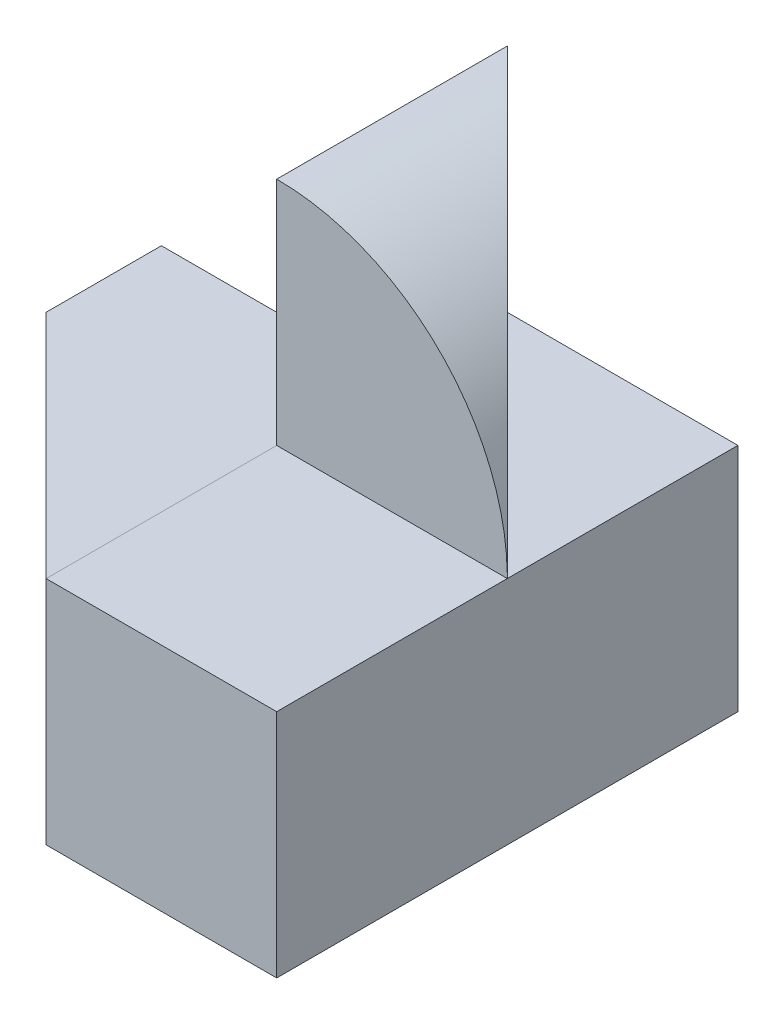
SolidWorks part; units mm, degrees
ref_plane "Front" through (0, 0, 0) normal (0, 0, 1) x (1, 0, 0)
ref_plane "Top" through (0, 0, 0) normal (0, 1, 0) x (1, 0, 0)
ref_plane "Right" through (0, 0, 0) normal (1, 0, 0) x (0, 0, -1)
sketch "Sketch1" plane through (0, 0, 0) normal (0, 1, 0) x (1, 0, 0)
  line L1 (-2, -2) -> (2, -2)
  line L2 (-2, -2) -> (-2, 2)
  line L3 (-2, 2) -> (2, 2)
  line L4 (2, -2) -> (2, 2)
  line L5 (-2, -2) -> (2, 2) construction
  line L6 (-2, 2) -> (2, -2) construction
  point P0 (0, 0)
  dimension "D1" = 4
  dimension "D2" = 4
extrude "Boss-Extrude1" add sketch "Sketch1" along normal blind 4
sketch "Sketch2" plane through (0, 0, 2) normal (0, 0, 1) x (1, 0, 0)
  line L0 (2, 4) -> (2, 0) construction
  line L1 (-2, 4) -> (2, 4) construction
  line L2 (0, 4) -> (0.0003, 2)
  line L3 (0.0003, 2) -> (-2, 2)
  line L4 (-2, 4) -> (-2, 0) construction
  line L5 (-2, 2) -> (-2, 4)
  line L6 (-2, 4) -> (2, 4)
  line L7 (2, 4) -> (2, 2.0349)
  arc A0 (2, 2.0349) -> (0, 4) centre (0.0003, 2) ccw
  line M2 (2, 0) -> (2, 4)
  line M3 (2, 4) -> (-2, 4)
  line M4 (-2, 4) -> (-2, 0)
  dimension "D1" = 2
extrude "Cut-Extrude1" cut sketch "Sketch2" against normal blind 4 contours L3 L2 M3 M4 | A0 M2 M3
sketch "Sketch3" plane through (0, 2, 0) normal (0, 1, 0) x (1, 0, 0)
  line L0 (0.0003, -2) -> (-2, 0)
  line L1 (-2, 2) -> (-2, -2) construction
  line L2 (-2, 0) -> (-2, -2)
  line L3 (-2, -2) -> (0.0003, -2)
  dimension "D1" = 2
extrude "Cut-Extrude2" cut sketch "Sketch3" against normal blind 4 contours L3 L0 L2
sketch "Sketch4" plane through (0.0006, 0, 0) normal (-1, -0.0002, 0) x (0, 0, 1)
  line L0 (-2, 2) -> (2, 2) construction
  line L1 (2, 4) -> (0, 4)
  line L2 (2, 4) -> (2, 2)
  line L3 (2, 2) -> (0, 2)
  line L4 (0, 4) -> (0, 2)
extrude "Cut-Extrude3" cut sketch "Sketch4" against normal blind 4
sketch "Sketch5" plane through (-0.0003, 2, 0) normal (-0.0002, 1, 0) x (1, 0.0002, 0)
  line L0 (2.0003, 0) -> (0.0009, 2)
  line L1 (0.0009, 2) -> (2.0003, 2)
  line L2 (2.0003, 2) -> (2.0003, 0)
extrude "Cut-Extrude4" cut sketch "Sketch5" along normal blind 10
sketch "Sketch6" plane through (0, 0, -2) normal (0, 0, -1) x (-1, 0, 0)
  line L0 (2, 0) -> (-0.0003, 2)
  line L1 (-0.0003, 2) -> (2, 2)
  line L2 (2, 2) -> (2, 0)
extrude "Cut-Extrude5" cut sketch "Sketch6" against normal blind 1
sketch "Sketch7" plane through (0, 0, 2) normal (0, 0, 1) x (1, 0, 0)
  line L0 (-2, 2) -> (-2, 0)
  line L1 (-2, 0) -> (0.0003, 0)
  arc A0 (0.0003, 0) -> (-2, 2) centre (0, 2) cw
extrude "Cut-Extrude6" cut sketch "Sketch7" against normal blind 2
